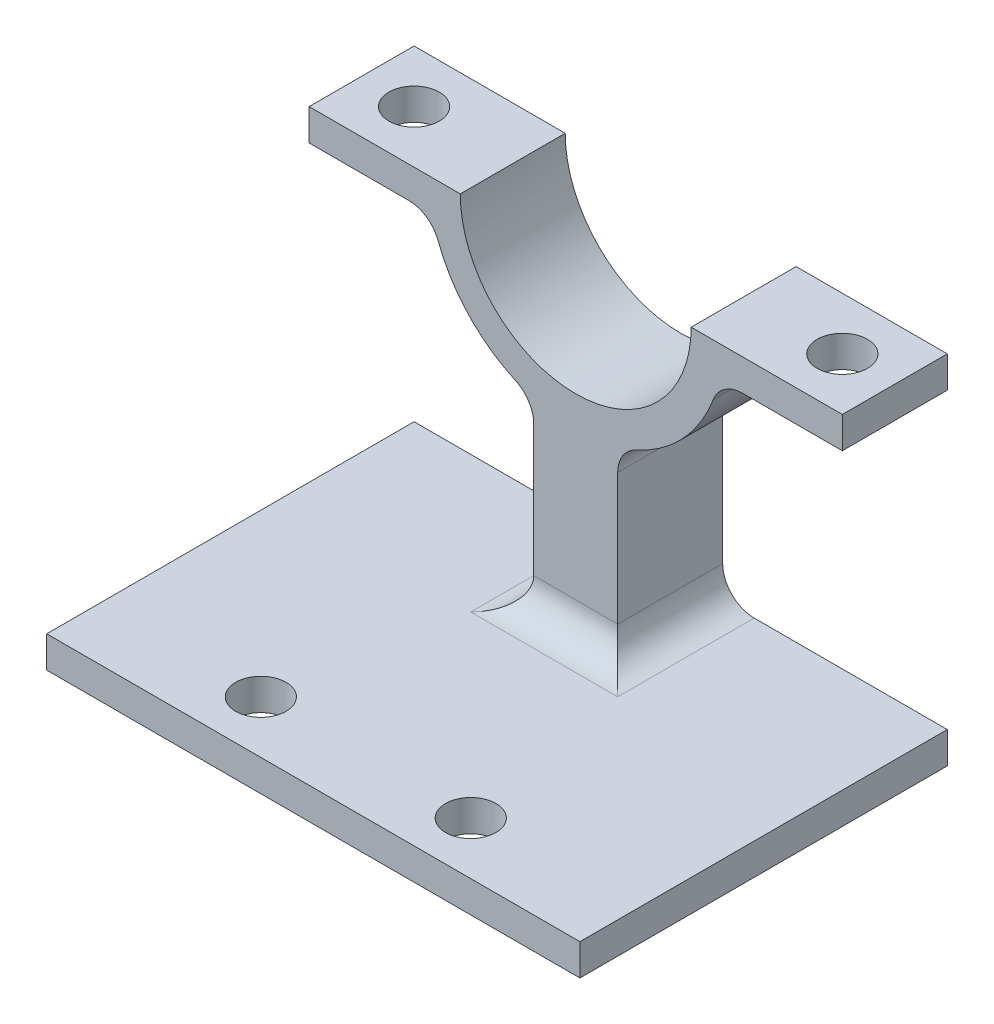
SolidWorks part; units mm, degrees
material "6061-T6 (SS)"
ref_plane "Front Plane" through (0, 0, 0) normal (0, 0, 1) x (1, 0, 0)
ref_plane "Top Plane" through (0, 0, 0) normal (0, 1, 0) x (1, 0, 0)
ref_plane "Right Plane" through (0, 0, 0) normal (1, 0, 0) x (0, 0, -1)
sketch "Sketch1" plane through (0, 0, 0) normal (0, 0, 1) x (1, 0, 0)
  line L0 (5.5, 0) -> (12.7, 0)
  line L1 (12.7, 0) -> (12.7, -1.5)
  line L2 (12.7, -1.5) -> (6.8374, -1.5)
  line L5 (0, 0) -> (0, -7) construction
  line L7 (-12.7, -1.5) -> (-6.8374, -1.5)
  line L8 (-12.7, 0) -> (-12.7, -1.5)
  line L9 (-5.5, 0) -> (-12.7, 0)
  arc A2 (5.5, 0) -> (-5.5, 0) centre (0, 0) cw
  arc A3 (-6.8374, -1.5) -> (6.8374, -1.5) centre (0, 0) ccw
  dimension "D1" = 7
  dimension "D2" = 5.5
  dimension "D3" = 12.7
  dimension "D4" = 1.5
extrude "Boss-Extrude1" add sketch "Sketch1" along normal mid plane 5
sketch "Sketch2" plane through (0, 0, 0) normal (0, 1, 0) x (1, 0, 0)
  line L0 (12.7, 0) -> (-12.7, 0) construction
  line L1 (-12.7, -2.5) -> (-12.7, 2.5) construction
  line L2 (0, 0) -> (0, 2.5) construction
  line L3 (5.5, 2.5) -> (-5.5, 2.5) construction
  circle A0 centre (-10.2, 0) radius 1.2
  circle A1 centre (10.2, 0) radius 1.2
  dimension "D1" = 2.5
  dimension "D2" = 2.4
extrude "Cut-Extrude1" cut sketch "Sketch2" against normal through all
sketch "Sketch3" plane through (0, 0, 0) normal (0, 1, 0) x (1, 0, 0)
  line L0 (5.5, -2.5) -> (5.5, 2.5) construction
  line L1 (-2, -2.5) -> (2, -2.5)
  line L2 (-2, -2.5) -> (-2, 2.5)
  line L3 (-2, 2.5) -> (2, 2.5)
  line L4 (2, -2.5) -> (2, 2.5)
  line L5 (-2, -2.5) -> (2, 2.5) construction
  line L6 (-2, 2.5) -> (2, -2.5) construction
  point P0 (0, 0)
  dimension "D1" = 4
extrude "Boss-Extrude2" add sketch "Sketch3" along normal up to surface (8.7918 mm away) from offset 15.5
sketch "Sketch4" plane through (0, -15.5, 0) normal (0, -1, 0) x (1, 0, 0)
  line L0 (0, 0) -> (0, 15) construction
  line L6 (0, 0) -> (0, -2.5) construction
  line L7 (2, -2.5) -> (-2, -2.5) construction
  line L12 (12.7, -2.5) -> (-12.7, -2.5)
  line L22 (-12.7, -2.5) -> (-12.7, 15)
  line L23 (-12.7, 15) -> (12.7, 15)
  line L24 (12.7, -2.5) -> (12.7, 15)
  line L27 (-5.5, 2.5) -> (-12.7, 2.5) construction
  dimension "D1" = 12.5
extrude "Boss-Extrude3" add sketch "Sketch4" along normal blind 1.5
fillet "Fillet1" radius 1.5 7 edges at (2, -15.5, 0) (2, -6.7082, 0) (6.8374, -1.5, 0) (-6.8374, -1.5, 0) (-2, -6.7082, 0) (-2, -15.5, 0) (0, -15.5, 2.5)
sketch "Sketch5" plane through (0, 0, 0) normal (0, 1, 0) x (1, 0, 0)
  line L0 (-5, 2.5) -> (-5, -15) construction
  line L1 (12.7, -15) -> (-12.7, -15) construction
  line L2 (0, 2.5) -> (0, -15) construction
  line L3 (5, 2.5) -> (5, -15) construction
  line L4 (5.5, 2.5) -> (-5.5, 2.5) construction
  line L5 (-5.5, 2.5) -> (-12.7, 2.5) construction
  circle A0 centre (-5, -12.5) radius 1.2
  circle A3 centre (5, -12.5) radius 1.2
  dimension "D2" = 2.4
  dimension "D1" = 2.5
  dimension "D4" = 5
extrude "Cut-Extrude2" cut sketch "Sketch5" against normal through all
